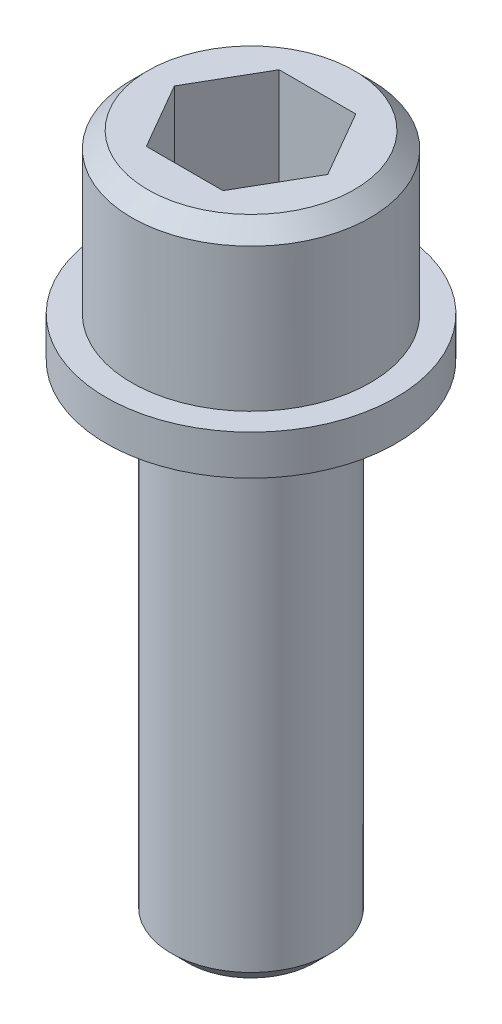
SolidWorks part; units mm, degrees
ref_plane "Front Plane" through (0, 0, 0) normal (0, 0, 1) x (1, 0, 0)
ref_plane "Top Plane" through (0, 0, 0) normal (0, 1, 0) x (1, 0, 0)
ref_plane "Right Plane" through (0, 0, 0) normal (1, 0, 0) x (0, 0, -1)
sketch "Sketch2" plane through (0, 0, 0) normal (0, 0, 1) x (1, 0, 0)
  line L0 (0, 0) -> (0, 41.275) construction
  line L1 (0, 41.275) -> (7.1437, 41.275)
  line L2 (7.1437, 41.275) -> (7.1437, 31.75)
  line L3 (7.1437, 31.75) -> (8.6741, 31.75)
  line L4 (8.6741, 31.75) -> (8.6741, 29.3624)
  line L5 (8.6741, 29.3624) -> (4.7625, 29.3624)
  line L6 (4.7625, 29.3624) -> (4.7625, 0)
  line L7 (4.7625, 0) -> (0, 0)
  line L8 (0, 0) -> (0, 41.275)
  dimension "D1" = 9.525
  dimension "D2" = 17.3482
  dimension "D3" = 14.2875
  dimension "D4" = 41.275
  dimension "D5" = 9.525
  dimension "D6" = 2.3876
revolve "Revolve1" add sketch "Sketch2" angle 360 about L0
sketch "Sketch3" plane through (0, 41.275, 0) normal (0, 1, 0) x (1, 0, 0)
  line L1 (4.5901, 0) -> (2.295, 3.9751)
  line L2 (2.295, 3.9751) -> (-2.295, 3.9751)
  line L3 (-2.295, 3.9751) -> (-4.5901, 0)
  line L4 (-4.5901, 0) -> (-2.295, -3.9751)
  line L5 (-2.295, -3.9751) -> (2.295, -3.9751)
  line L6 (2.295, -3.9751) -> (4.5901, 0)
  circle A3 centre (0, 0) radius 3.9751 construction
  dimension "D1" = 7.9502
extrude "Cut-Extrude1" cut sketch "Sketch3" against normal blind 6.35
chamfer "Chamfer1" distance 0.9652 angle 45 1 edges at (0, 41.275, -7.1437)
chamfer "Chamfer2" distance 0.9652 angle 45 1 edges at (0, 0, -4.7625)
